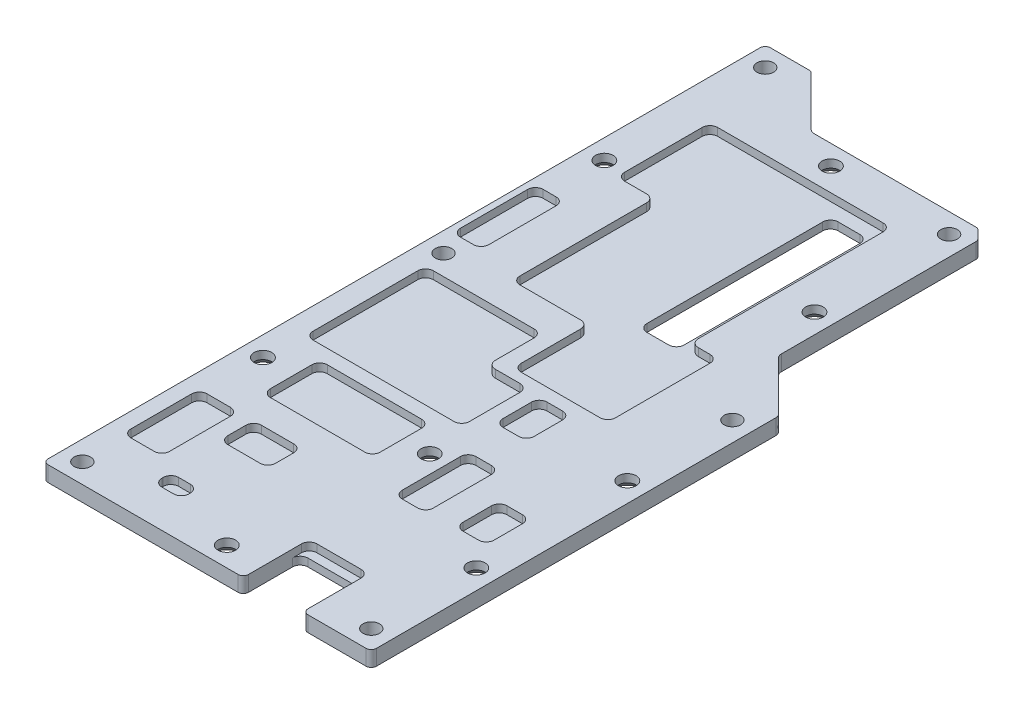
SolidWorks part; units mm, degrees
ref_plane "Front Plane" through (0, 0, 0) normal (0, 0, 1) x (1, 0, 0)
ref_plane "Top Plane" through (0, 0, 0) normal (0, 1, 0) x (1, 0, 0)
ref_plane "Right Plane" through (0, 0, 0) normal (1, 0, 0) x (0, 0, -1)
sketch "Sketch1" plane through (0, 0, 0) normal (0, 1, 0) x (1, 0, 0)
  line L0 (0, 1) -> (0, 138.7)
  line L1 (1, 0) -> (37.75, 0)
  line L2 (63.5, 1) -> (63.5, 78.3258)
  line L3 (1, 139.7) -> (8.4758, 139.7)
  line L4 (19.6713, 129.54) -> (50.8958, 129.54)
  line L5 (9.1829, 139.4071) -> (18.6107, 129.9793)
  line L6 (53.34, 89.5213) -> (53.34, 127.0958)
  line L7 (63.2071, 79.0329) -> (53.7793, 88.4607)
  line L8 (51.6029, 129.2471) -> (53.0471, 127.8029)
  line L13 (38.75, 1) -> (38.75, 9.5)
  line L14 (40.25, 11) -> (48.75, 11)
  line L15 (50.25, 9.5) -> (50.25, 1)
  line L16 (51.25, 0) -> (62.5, 0)
  arc A2 (1, 0) -> (0, 1) centre (1, 1) cw
  arc A3 (63.5, 1) -> (62.5, 0) centre (62.5, 1) cw
  arc A4 (53.7793, 88.4607) -> (53.34, 89.5213) centre (54.84, 89.5213) cw
  arc A5 (18.6107, 129.9793) -> (19.6713, 129.54) centre (19.6713, 131.04) ccw
  arc A6 (63.5, 78.3258) -> (63.2071, 79.0329) centre (62.5, 78.3258) ccw
  arc A7 (53.34, 127.0958) -> (53.0471, 127.8029) centre (52.34, 127.0958) ccw
  arc A8 (51.6029, 129.2471) -> (50.8958, 129.54) centre (50.8958, 128.54) ccw
  arc A9 (9.1829, 139.4071) -> (8.4758, 139.7) centre (8.4758, 138.7) ccw
  arc A10 (1, 139.7) -> (0, 138.7) centre (1, 138.7) ccw
  arc A13 (48.75, 11) -> (50.25, 9.5) centre (48.75, 9.5) cw
  arc A14 (38.75, 9.5) -> (40.25, 11) centre (40.25, 9.5) cw
  arc A15 (50.25, 1) -> (51.25, 0) centre (51.25, 1) ccw
  arc A16 (38.75, 1) -> (37.75, 0) centre (37.75, 1) cw
  point P20 (0, 0)
  point P23 (63.5, 0)
  point P26 (53.34, 88.9)
  point P29 (19.05, 129.54)
  point P32 (63.5, 78.74)
  point P35 (53.34, 127.51)
  point P38 (51.31, 129.54)
  point P41 (8.89, 139.7)
  point P44 (0, 139.7)
  point P45 (38.75, 11)
  point P48 (50.25, 0)
  point P51 (38.75, 0)
  dimension "D14" = 1.5
  dimension "D15" = 1
  dimension "D16" = 1
  dimension "D17" = 1.5
  dimension "D18" = 1
  dimension "D19" = 1
  dimension "D1" = 139.7
  dimension "D2" = 63.5
  dimension "D3" = 78.74
  dimension "D4" = 8.89
  dimension "D5" = 10.16
  dimension "D6" = 10.16
  dimension "D7" = 32.26
  dimension "D8" = 10.16
  dimension "D9" = 10.16
  dimension "D10" = 2.03
  dimension "D11" = 13.25
  dimension "D12" = 11.5
  dimension "D13" = 11
extrude "Boss-Extrude1" add sketch "Sketch1" along normal blind 3
sketch "Sketch2" plane through (0, 3, 0) normal (0, 1, 0) x (1, 0, 0)
  line L36 (50.25, 0) -> (50.25, 11.25)
  line L37 (51.25, 0) -> (62.5, 0) construction
  line L38 (48.75, 12.75) -> (40.25, 12.75)
  line L39 (38.75, 11.25) -> (38.75, 0)
  line L40 (1, 0) -> (37.75, 0) construction
  line L41 (38.75, 0) -> (50.25, 0)
  line L42 (63.5, 1) -> (63.5, 78.3258) construction
  line L43 (0, 138.7) -> (0, 1) construction
  line L44 (52.25, 37.5) -> (55.25, 37.5)
  line L45 (50.75, 36) -> (50.75, 30.5)
  line L46 (52.25, 29) -> (55.25, 29)
  line L47 (56.75, 36) -> (56.75, 30.5)
  line L48 (41, 42.75) -> (44, 42.75)
  line L49 (39.5, 41.25) -> (39.5, 30)
  line L50 (41, 28.5) -> (44, 28.5)
  line L51 (45.5, 41.25) -> (45.5, 30)
  line L52 (11.25, 43.75) -> (29.5, 43.75)
  line L53 (9.75, 42.25) -> (9.75, 34.25)
  line L54 (11.25, 32.75) -> (29.5, 32.75)
  line L55 (31, 42.25) -> (31, 34.25)
  line L56 (18, 10.5) -> (15.75, 10.5)
  line L57 (19.5, 9) -> (19.5, 8.75)
  line L58 (18, 7.25) -> (15.75, 7.25)
  line L59 (14.25, 9) -> (14.25, 8.75)
  line L60 (4.25, 68.25) -> (4.25, 48)
  line L61 (4.5, 27.25) -> (9, 27.25)
  line L62 (3, 25.75) -> (3, 14)
  line L63 (4.5, 12.5) -> (9, 12.5)
  line L64 (10.5, 25.75) -> (10.5, 14)
  line L65 (15, 27.25) -> (21.25, 27.25)
  line L66 (13.5, 25.75) -> (13.5, 22.25)
  line L67 (15, 20.75) -> (21.25, 20.75)
  line L68 (22.75, 25.75) -> (22.75, 22.25)
  line L69 (5.75, 46.5) -> (33, 46.5)
  line L70 (34.5, 48) -> (34.5, 57.75)
  line L71 (33, 59.25) -> (28.25, 59.25)
  line L72 (26.75, 60.75) -> (26.75, 68.25)
  line L73 (25.25, 69.75) -> (5.75, 69.75)
  line L74 (31.25, 61.25) -> (46.5, 61.25)
  line L75 (38.75, 58.75) -> (41.75, 58.75)
  line L76 (37.25, 57.25) -> (37.25, 51.75)
  line L77 (38.75, 50.25) -> (41.75, 50.25)
  line L78 (43.25, 57.25) -> (43.25, 51.75)
  line L79 (48, 62.75) -> (48, 81)
  line L80 (46.5, 82.5) -> (44.25, 82.5)
  line L81 (42.75, 84) -> (42.75, 119.75)
  line L82 (41.25, 121.25) -> (9.25, 121.25)
  line L83 (7.75, 119.75) -> (7.75, 104.75)
  line L84 (9.25, 103.25) -> (13.5, 103.25)
  line L85 (15, 101.75) -> (15, 77.25)
  line L86 (16.5, 75.75) -> (28.25, 75.75)
  line L87 (29.75, 74.25) -> (29.75, 62.75)
  line L89 (2.75, 94) -> (5.25, 94)
  line L90 (1.25, 92.5) -> (1.25, 79.5)
  line L91 (2.75, 78) -> (5.25, 78)
  line L92 (6.75, 92.5) -> (6.75, 79.5)
  arc A32 (50.25, 11.25) -> (48.75, 12.75) centre (48.75, 11.25) ccw
  arc A33 (40.25, 12.75) -> (38.75, 11.25) centre (40.25, 11.25) ccw
  arc A34 (50.75, 30.5) -> (52.25, 29) centre (52.25, 30.5) ccw
  arc A35 (55.25, 29) -> (56.75, 30.5) centre (55.25, 30.5) ccw
  arc A36 (56.75, 36) -> (55.25, 37.5) centre (55.25, 36) ccw
  arc A37 (50.75, 36) -> (52.25, 37.5) centre (52.25, 36) cw
  arc A38 (39.5, 30) -> (41, 28.5) centre (41, 30) ccw
  arc A39 (44, 28.5) -> (45.5, 30) centre (44, 30) ccw
  arc A40 (44, 42.75) -> (45.5, 41.25) centre (44, 41.25) cw
  arc A41 (41, 42.75) -> (39.5, 41.25) centre (41, 41.25) ccw
  arc A42 (29.5, 43.75) -> (31, 42.25) centre (29.5, 42.25) cw
  arc A43 (29.5, 32.75) -> (31, 34.25) centre (29.5, 34.25) ccw
  arc A44 (9.75, 34.25) -> (11.25, 32.75) centre (11.25, 34.25) ccw
  arc A45 (11.25, 43.75) -> (9.75, 42.25) centre (11.25, 42.25) ccw
  arc A46 (19.5, 8.75) -> (18, 7.25) centre (18, 8.75) cw
  arc A47 (18, 10.5) -> (19.5, 9) centre (18, 9) cw
  arc A48 (15.75, 7.25) -> (14.25, 8.75) centre (15.75, 8.75) cw
  arc A49 (15.75, 10.5) -> (14.25, 9) centre (15.75, 9) ccw
  arc A50 (21.25, 20.75) -> (22.75, 22.25) centre (21.25, 22.25) ccw
  arc A51 (21.25, 27.25) -> (22.75, 25.75) centre (21.25, 25.75) cw
  arc A52 (15, 27.25) -> (13.5, 25.75) centre (15, 25.75) ccw
  arc A53 (13.5, 22.25) -> (15, 20.75) centre (15, 22.25) ccw
  arc A54 (3, 14) -> (4.5, 12.5) centre (4.5, 14) ccw
  arc A55 (9, 12.5) -> (10.5, 14) centre (9, 14) ccw
  arc A56 (9, 27.25) -> (10.5, 25.75) centre (9, 25.75) cw
  arc A57 (4.5, 27.25) -> (3, 25.75) centre (4.5, 25.75) ccw
  arc A58 (26.75, 68.25) -> (25.25, 69.75) centre (25.25, 68.25) ccw
  arc A59 (34.5, 57.75) -> (33, 59.25) centre (33, 57.75) ccw
  arc A60 (33, 46.5) -> (34.5, 48) centre (33, 48) ccw
  arc A61 (4.25, 48) -> (5.75, 46.5) centre (5.75, 48) ccw
  arc A62 (5.75, 69.75) -> (4.25, 68.25) centre (5.75, 68.25) ccw
  arc A63 (28.25, 59.25) -> (26.75, 60.75) centre (28.25, 60.75) cw
  arc A64 (41.75, 58.75) -> (43.25, 57.25) centre (41.75, 57.25) cw
  arc A65 (41.75, 50.25) -> (43.25, 51.75) centre (41.75, 51.75) ccw
  arc A66 (37.25, 51.75) -> (38.75, 50.25) centre (38.75, 51.75) ccw
  arc A67 (38.75, 58.75) -> (37.25, 57.25) centre (38.75, 57.25) ccw
  arc A68 (42.75, 119.75) -> (41.25, 121.25) centre (41.25, 119.75) ccw
  arc A69 (44.25, 82.5) -> (42.75, 84) centre (44.25, 84) cw
  arc A70 (48, 81) -> (46.5, 82.5) centre (46.5, 81) ccw
  arc A71 (46.5, 61.25) -> (48, 62.75) centre (46.5, 62.75) ccw
  arc A72 (31.25, 61.25) -> (29.75, 62.75) centre (31.25, 62.75) cw
  arc A73 (28.25, 75.75) -> (29.75, 74.25) centre (28.25, 74.25) cw
  arc A74 (15, 77.25) -> (16.5, 75.75) centre (16.5, 77.25) ccw
  arc A75 (13.5, 103.25) -> (15, 101.75) centre (13.5, 101.75) cw
  arc A76 (7.75, 104.75) -> (9.25, 103.25) centre (9.25, 104.75) ccw
  arc A77 (9.25, 121.25) -> (7.75, 119.75) centre (9.25, 119.75) ccw
  arc A78 (1.25, 79.5) -> (2.75, 78) centre (2.75, 79.5) ccw
  arc A79 (5.25, 78) -> (6.75, 79.5) centre (5.25, 79.5) ccw
  arc A80 (5.25, 94) -> (6.75, 92.5) centre (5.25, 92.5) cw
  arc A81 (2.75, 94) -> (1.25, 92.5) centre (2.75, 92.5) ccw
  point P12 (50.25, 12.75)
  point P15 (38.75, 12.75)
  point P22 (50.75, 29)
  point P25 (56.75, 29)
  point P28 (56.75, 37.5)
  point P37 (39.5, 28.5)
  point P40 (45.5, 28.5)
  point P43 (45.5, 42.75)
  point P56 (31, 32.75)
  point P59 (9.75, 32.75)
  point P62 (9.75, 43.75)
  point P69 (19.5, 7.25)
  point P72 (19.5, 10.5)
  point P77 (14.25, 10.5)
  point P90 (22.75, 27.25)
  point P93 (13.5, 27.25)
  point P96 (13.5, 20.75)
  point P99 (3, 12.5)
  point P104 (10.5, 27.25)
  point P107 (3, 27.25)
  point P117 (26.75, 69.75)
  point P120 (34.5, 59.25)
  point P123 (34.5, 46.5)
  point P126 (4.25, 46.5)
  point P129 (4.25, 69.75)
  point P137 (43.25, 58.75)
  point P142 (37.25, 50.25)
  point P145 (37.25, 58.75)
  point P158 (42.75, 121.25)
  point P161 (42.75, 82.5)
  point P164 (48, 82.5)
  point P167 (48, 61.25)
  point P170 (29.75, 61.25)
  point P175 (15, 75.75)
  point P178 (15, 103.25)
  point P181 (7.75, 103.25)
  point P184 (7.75, 121.25)
  point P192 (1.25, 78)
  point P197 (6.75, 94)
  point P200 (1.25, 94)
  dimension "D35" = 30.25
  dimension "D36" = 12.75
  dimension "D37" = 22.5
  dimension "D38" = 4.25
  dimension "D39" = 46.5
  dimension "D40" = 1.5
  dimension "D41" = 1.5
  dimension "D42" = 8.5
  dimension "D4" = 1.5
  dimension "D9" = 1.5
  dimension "D14" = 1.5
  dimension "D19" = 1.5
  dimension "D24" = 1.5
  dimension "D33" = 1.5
  dimension "D46" = 1.5
  dimension "D57" = 1.5
  dimension "D62" = 1.5
  dimension "D1" = 13.25
  dimension "D2" = 12.75
  dimension "D3" = 11.5
  dimension "D5" = 6
  dimension "D6" = 8.5
  dimension "D7" = 6.75
  dimension "D8" = 29
  dimension "D10" = 14.25
  dimension "D11" = 6
  dimension "D12" = 18
  dimension "D13" = 28.5
  dimension "D15" = 21.25
  dimension "D16" = 11
  dimension "D17" = 32.75
  dimension "D18" = 9.75
  dimension "D20" = 3.25
  dimension "D21" = 5.25
  dimension "D22" = 7.25
  dimension "D23" = 14.25
  dimension "D25" = 14.75
  dimension "D26" = 7.5
  dimension "D27" = 12.5
  dimension "D28" = 3
  dimension "D29" = 6.5
  dimension "D30" = 9.25
  dimension "D31" = 13.5
  dimension "D32" = 20.75
  dimension "D34" = 23.25
  dimension "D43" = 6
  dimension "D44" = 20.25
  dimension "D45" = 50.25
  dimension "D47" = 18.25
  dimension "D48" = 21.25
  dimension "D49" = 5.25
  dimension "D50" = 38.75
  dimension "D51" = 35
  dimension "D52" = 18
  dimension "D53" = 7.25
  dimension "D54" = 27.5
  dimension "D55" = 15.5
  dimension "D56" = 61.25
  dimension "D58" = 16
  dimension "D59" = 5.5
  dimension "D60" = 1.25
  dimension "D61" = 78
extrude "Cut-Extrude1" cut sketch "Sketch2" against normal blind 1.5
sketch "Sketch3" plane through (0, 0, 0) normal (0, -1, 0) x (-1, 0, 0)
  line L0 (-37.34, 118.58) -> (-37.34, 81.58) construction
  line L1 (-39.44, 118.58) -> (-35.24, 118.58)
  line L2 (-40.94, 117.08) -> (-40.94, 83.08)
  line L3 (-39.44, 81.58) -> (-35.24, 81.58)
  line L4 (-33.74, 117.08) -> (-33.74, 83.08)
  line L5 (-40.94, 100.08) -> (-33.74, 100.08) construction
  arc A0 (-40.94, 83.08) -> (-39.44, 81.58) centre (-39.44, 83.08) ccw
  arc A1 (-35.24, 81.58) -> (-33.74, 83.08) centre (-35.24, 83.08) ccw
  arc A2 (-35.24, 118.58) -> (-33.74, 117.08) centre (-35.24, 117.08) cw
  arc A3 (-39.44, 118.58) -> (-40.94, 117.08) centre (-39.44, 117.08) ccw
  point P12 (-40.94, 81.58)
  point P17 (-33.74, 118.58)
  point P20 (-40.94, 118.58)
  dimension "D5" = 1.5
  dimension "D1" = 37
  dimension "D2" = 7.2
  dimension "D3" = 37.34
  dimension "D4" = 100.08
extrude "Cut-Extrude2" cut sketch "Sketch3" against normal up to next
hole_wizard "Ø3.2 (3.2) Diameter Hole1" positions "Sketch5" profile "Sketch6" hole size "Ø3.2" standard "ISO" end condition through all
sketch "Sketch5" plane through (0, 3, 0) normal (0, 1, 0) x (1, 0, 0)
  line L0 (51.25, 0) -> (62.5, 0) construction
  line L1 (63.5, 1) -> (63.5, 78.3258) construction
  line L2 (53.34, 89.5213) -> (53.34, 127.0958) construction
  line L3 (50.8958, 129.54) -> (19.6713, 129.54) construction
  line L4 (0, 138.7) -> (0, 1) construction
  line L5 (8.4758, 139.7) -> (1, 139.7) construction
  line L6 (1, 0) -> (37.75, 0) construction
  point P0 (3.81, 135.89)
  point P2 (49.53, 125.73)
  point P4 (59.69, 73.66)
  point P6 (59.69, 3.81)
  point P8 (3.81, 3.81)
  point P10 (3.81, 73.66)
  dimension "D1" = 3.81
  dimension "D2" = 3.81
  dimension "D3" = 3.81
  dimension "D4" = 3.81
  dimension "D5" = 3.81
  dimension "D6" = 3.81
  dimension "D7" = 3.81
  dimension "D8" = 3.81
  dimension "D9" = 3.81
  dimension "D10" = 3.81
  dimension "D11" = 69.85
  dimension "D12" = 69.85
sketch "Sketch6" plane through (3.81, 3, -135.89) normal (1, 0, 0) x (0, 0, 1)
  line L0 (0, 0) -> (0, 3)
  line L1 (0, 3) -> (1.6, 3)
  line L2 (1.6, 3) -> (1.6, 0)
  line L5 (1.6, 0) -> (0, 0)
  line L11 (0, -6.35) -> (0, 107.95) construction
  dimension "Thru Hole Dia." = 3.2
  dimension "Thru Hole Depth" = 3
hole_wizard "CSK for M3 Countersunk Raised Head Screw1" positions "Sketch7" profile "Sketch8" countersink size "M3" standard "ISO" end condition through all
sketch "Sketch7" plane through (0, 0, 0) normal (0, -1, 0) x (-1, 0, 0)
  line L0 (0, 138.7) -> (0, 1) construction
  line L1 (-50.8958, 129.54) -> (-19.6713, 129.54) construction
  line L2 (-1, 0) -> (-37.75, 0) construction
  line L3 (-63.5, 1) -> (-63.5, 78.3258) construction
  line L4 (-53.34, 89.5213) -> (-53.34, 127.0958) construction
  circle A0 centre (-59.69, 3.81) radius 1.6 construction
  circle A2 centre (-3.81, 3.81) radius 1.6 construction
  circle A3 centre (-3.81, 135.89) radius 1.6 construction
  circle A4 centre (-49.53, 125.73) radius 1.6 construction
  point P0 (-26.67, 125.73)
  point P2 (-31.75, 3.81)
  point P4 (-59.69, 53.34)
  point P6 (-3.81, 38.74)
  point P8 (-36.07, 38.74)
  point P10 (-59.69, 24.13)
  point P12 (-49.53, 99.69)
  point P14 (-3.81, 104.77)
  dimension "D1" = 3.81
  dimension "D2" = 3.81
  dimension "D3" = 3.81
  dimension "D4" = 3.81
  dimension "D5" = 3.81
  dimension "D6" = 3.81
  dimension "D7" = 3.81
  dimension "D8" = 49.53
  dimension "D9" = 20.32
  dimension "D10" = 32.26
  dimension "D11" = 27.94
  dimension "D12" = 34.93
  dimension "D13" = 31.12
  dimension "D14" = 26.04
  dimension "D15" = 22.86
sketch "Sketch8" plane through (26.67, 0, -125.73) normal (1, 0, 0) x (0, 0, -1)
  line L0 (0, 0) -> (0, 3)
  line L1 (0, 3) -> (1.7, 3)
  line L2 (1.7, 3) -> (1.7, 1.45)
  line L3 (1.7, 1.45) -> (3.15, 0)
  line L5 (3.15, 0) -> (0, 0)
  line L6 (-1.7, 1.45) -> (-3.15, 0) construction
  line L11 (0, -6.35) -> (0, 107.95) construction
  dimension "Thru Hole Dia." = 3.4
  dimension "Thru Hole Depth" = 3
  dimension "Near C'Sink Dia." = 6.3
  dimension "Near C'Sink Angle" = 90
